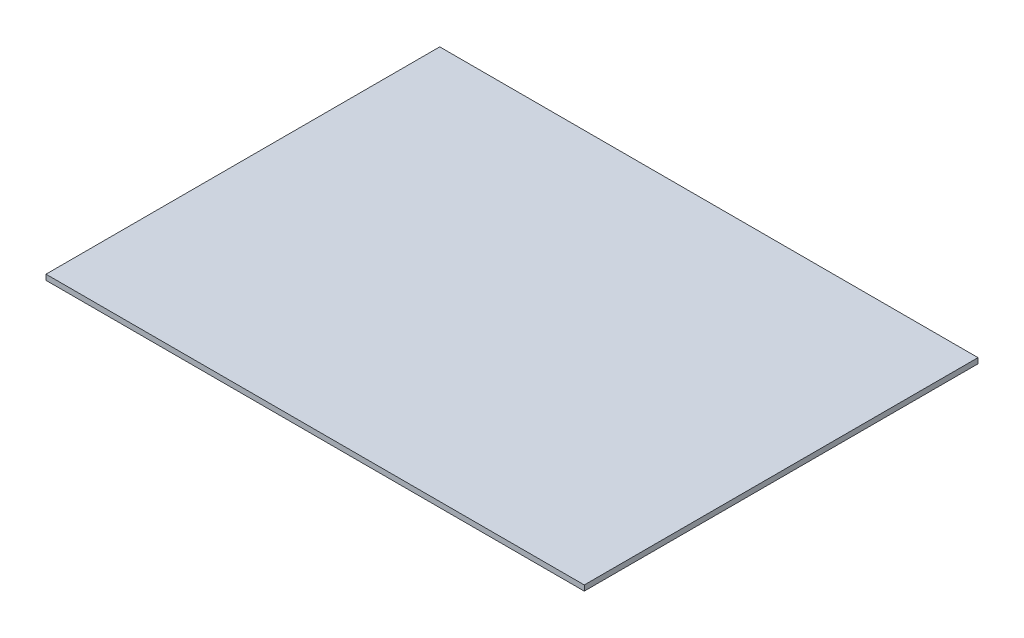
SolidWorks part; units mm, degrees
material "1060 Alloy"
ref_plane "Front Plane" through (0, 0, 0) normal (0, 0, 1) x (1, 0, 0)
ref_plane "Top Plane" through (0, 0, 0) normal (0, 1, 0) x (1, 0, 0)
ref_plane "Right Plane" through (0, 0, 0) normal (1, 0, 0) x (0, 0, -1)
sketch "Sketch1" plane through (0, 0, 0) normal (0, 1, 0) x (1, 0, 0)
  line L1 (0, 0) -> (200, 0)
  line L2 (0, 0) -> (0, 146.2931)
  line L3 (0, 146.2931) -> (200, 146.2931)
  line L4 (200, 0) -> (200, 146.2931)
  dimension "D1" = 200
extrude "Boss-Extrude2" add sketch "Sketch1" along normal blind 2
